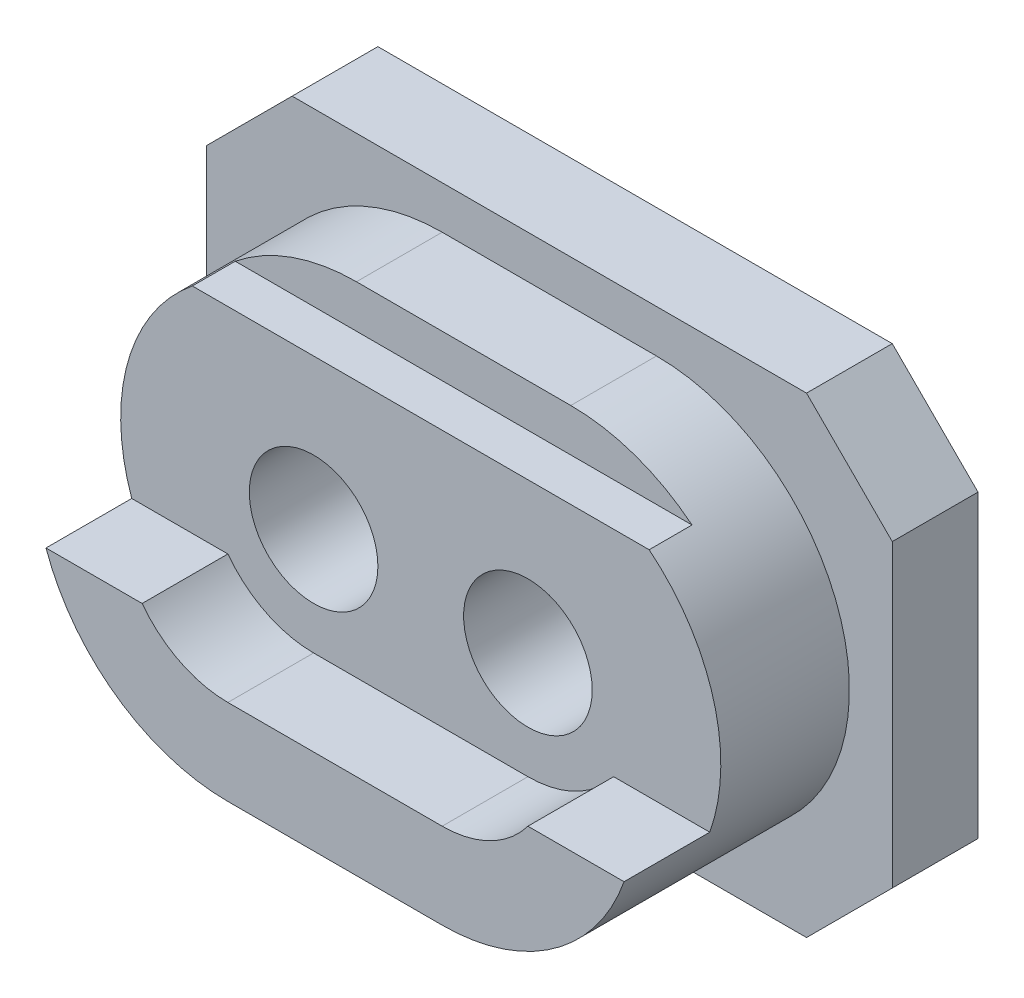
SolidWorks part; units mm, degrees
ref_plane "Front" through (0, 0, 0) normal (0, 0, 1) x (1, 0, 0)
ref_plane "Top" through (0, 0, 0) normal (0, 1, 0) x (1, 0, 0)
ref_plane "Right" through (0, 0, 0) normal (1, 0, 0) x (0, 0, -1)
sketch "Sketch1" plane through (0, 0, 0) normal (0, 0, 1) x (1, 0, 0)
  line L0 (-8, 3.5) -> (-6, 5.5)
  line L1 (-6, -5.5) -> (6, -5.5)
  line L2 (-8, -3.5) -> (-8, 3.5)
  line L3 (-6, 5.5) -> (6, 5.5)
  line L4 (8, -3.5) -> (8, 3.5)
  line L5 (-8, -5.5) -> (8, 5.5) construction
  line L6 (-8, 5.5) -> (8, -5.5) construction
  line L7 (6, 5.5) -> (8, 3.5)
  line L8 (6, -5.5) -> (8, -3.5)
  line L9 (-8, -3.5) -> (-6, -5.5)
  circle A0 centre (-2.5, 0) radius 1.5
  circle A1 centre (2.5, 0) radius 1.5
  point P0 (0, 0)
  dimension "D3" = 3
  dimension "D4" = 3
  dimension "D1" = 16
  dimension "D2" = 11
  dimension "D9" = 2.5
  dimension "D10" = 2.5
extrude "Boss-Extrude1" add sketch "Sketch1" along normal blind 2
sketch "Sketch2" plane through (0, 0, 2) normal (0, 0, 1) x (1, 0, 0)
  line L0 (-2.5, 0) -> (2.5, 0) construction
  line L1 (-2.5, 4.5) -> (2.5, 4.5)
  line L2 (-2.5, -4.5) -> (2.5, -4.5)
  arc A0 (-2.5, 4.5) -> (-2.5, -4.5) centre (-2.5, 0) ccw
  arc A1 (2.5, -4.5) -> (2.5, 4.5) centre (2.5, 0) ccw
  circle A2 centre (-2.5, 0) radius 1.5
  circle A3 centre (2.5, 0) radius 1.5
  point P4 (0, 0)
  dimension "D1" = 4.5
extrude "Boss-Extrude2" add sketch "Sketch2" along normal blind 5
sketch "Sketch4" plane through (0, 0, 7) normal (0, 0, 1) x (1, 0, 0)
  line L0 (-2.5, -2.5) -> (2.5, -2.5)
  line L1 (-4.8951, 3.5) -> (4.5401, 3.5)
  line L2 (4.5401, 3.5) -> (6.9803, 3.5)
  line L8 (4.5, -1.5) -> (7.2918, -1.5)
  line L9 (7.2918, -1.5) -> (6.9803, 3.5)
  line L11 (-6.6105, 3.5) -> (-4.8951, 3.5)
  line L12 (-4.5, -1.5) -> (-7.4821, -1.5)
  line L13 (-7.4821, -1.5) -> (-6.6105, 3.5)
  arc A0 (-4.5, -1.5) -> (-2.5, -2.5) centre (-2.5, 0) ccw
  arc A1 (2.5, -2.5) -> (4.5, -1.5) centre (2.5, 0) ccw
  circle A5 centre (2.5, 0) radius 1.5 construction
  circle A6 centre (-2.5, 0) radius 1.5 construction
  dimension "D1" = 2.5
  dimension "D2" = 1
  dimension "D3" = 3.5
  dimension "D4" = 1
extrude "Cut-Extrude1" cut sketch "Sketch4" against normal blind 2
sketch "Sketch5" plane through (-8, 0, 0) normal (-1, 0, 0) x (0, 0, 1)
  line L1 (7, 4.5) -> (4, 4.5)
  line L2 (7, 4.5) -> (7, 3.5)
  line L3 (7, 3.5) -> (4, 3.5)
  line L4 (4, 4.5) -> (4, 3.5)
  dimension "D1" = 1
  dimension "D2" = 3
extrude "Cut-Extrude2" cut sketch "Sketch5" against normal blind 22
